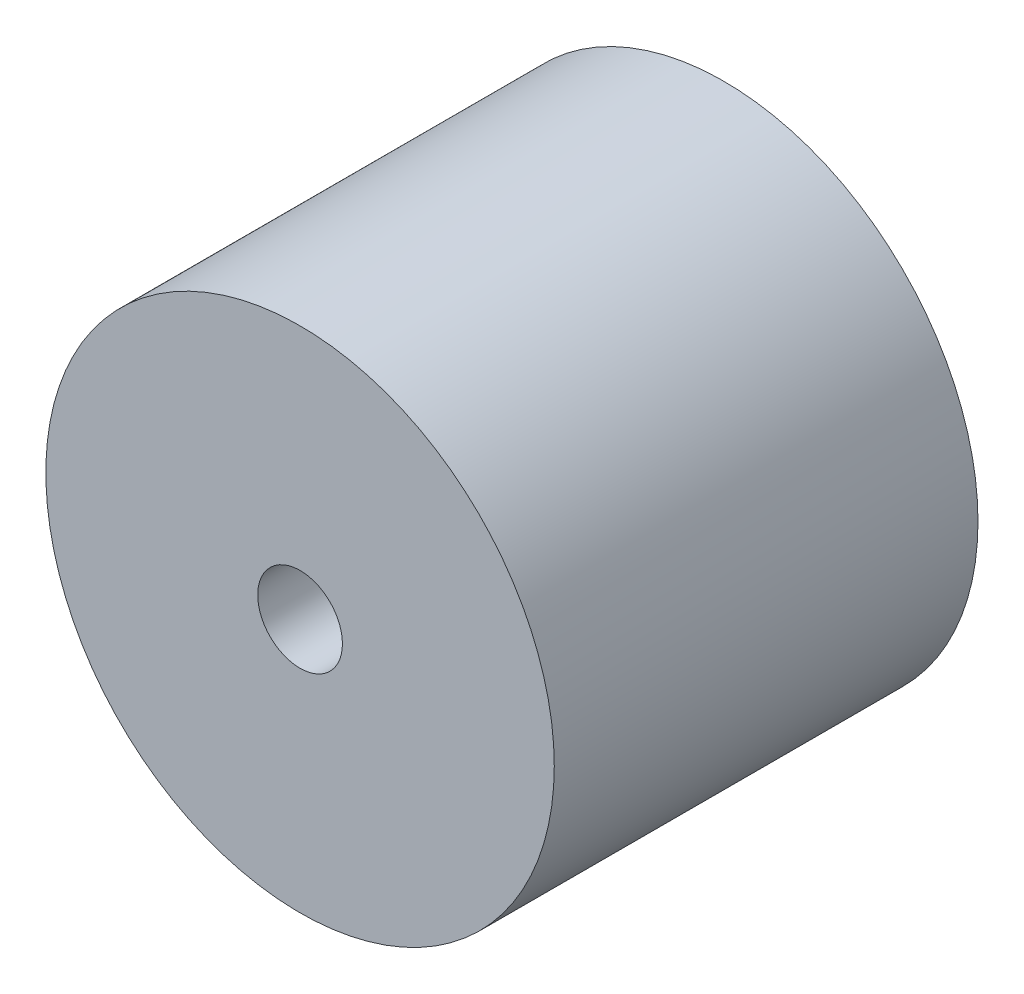
SolidWorks part; units mm, degrees
ref_plane "Front Plane" through (0, 0, 0) normal (0, 0, 1) x (1, 0, 0)
ref_plane "Top Plane" through (0, 0, 0) normal (0, 1, 0) x (1, 0, 0)
ref_plane "Right Plane" through (0, 0, 0) normal (1, 0, 0) x (0, 0, -1)
sketch "Sketch1" plane through (0, 0, 0) normal (0, 0, 1) x (1, 0, 0)
  circle A0 centre (0, 0) radius 18
  circle A1 centre (0, 0) radius 3
  dimension "D1" = 36
  dimension "D2" = 6
extrude "Boss-Extrude1" add sketch "Sketch1" along normal blind 30
